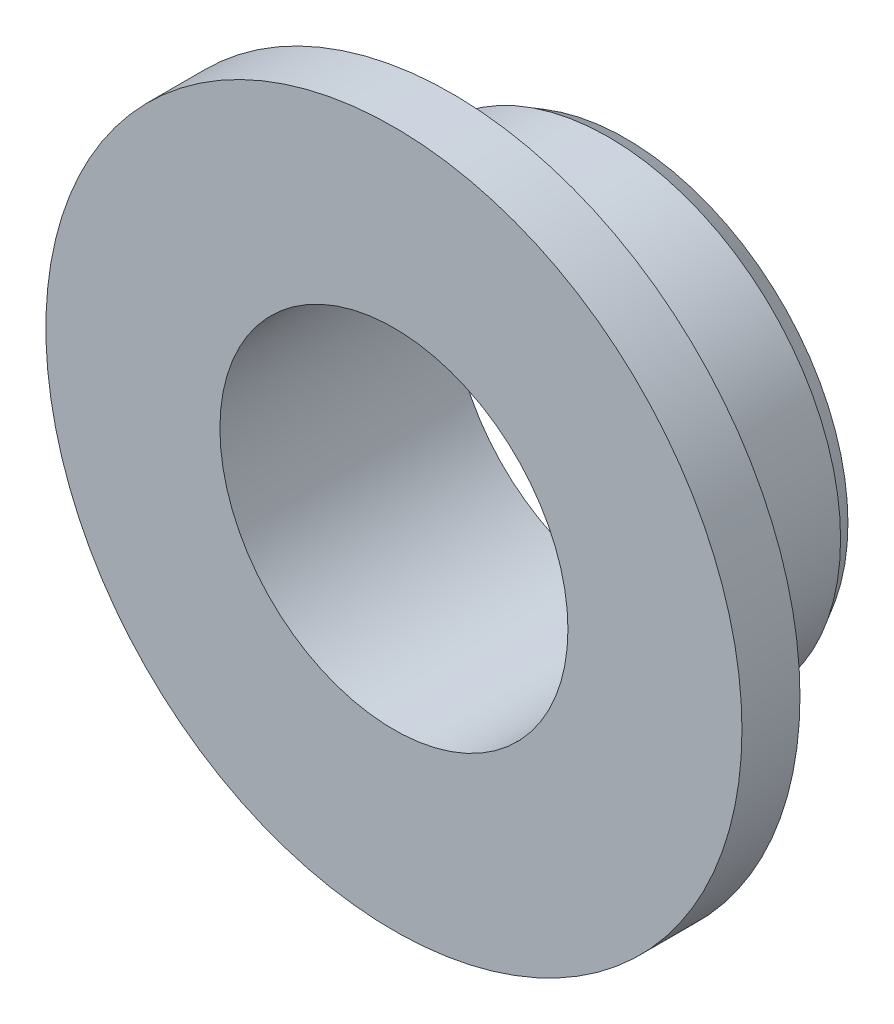
SolidWorks part; units mm, degrees
ref_plane "Front Plane" through (0, 0, 0) normal (0, 0, 1) x (1, 0, 0)
ref_plane "Top Plane" through (0, 0, 0) normal (0, 1, 0) x (1, 0, 0)
ref_plane "Right Plane" through (0, 0, 0) normal (1, 0, 0) x (0, 0, -1)
sketch "Sketch1" plane through (0, 0, 0) normal (0, 0, 1) x (1, 0, 0)
  circle A0 centre (0, 0) radius 3
  circle A1 centre (0, 0) radius 4
  dimension "D1" = 6
  dimension "D2" = 8
extrude "Boss-Extrude1" add sketch "Sketch1" along normal blind 4
sketch "Sketch2" plane through (0, 0, 4) normal (0, 0, 1) x (1, 0, 0)
  circle A0 centre (0, 0) radius 6
  circle A1 centre (0, 0) radius 3 construction
  circle A2 centre (0, 0) radius 3
  dimension "D1" = 12
extrude "Boss-Extrude2" add sketch "Sketch2" against normal blind 1
fillet "Fillet1" radius 0.5 1 edges at (4, 0, 3)
chamfer "Chamfer1" distance 0.3 angle 30 1 edges at (4, 0, 0)
